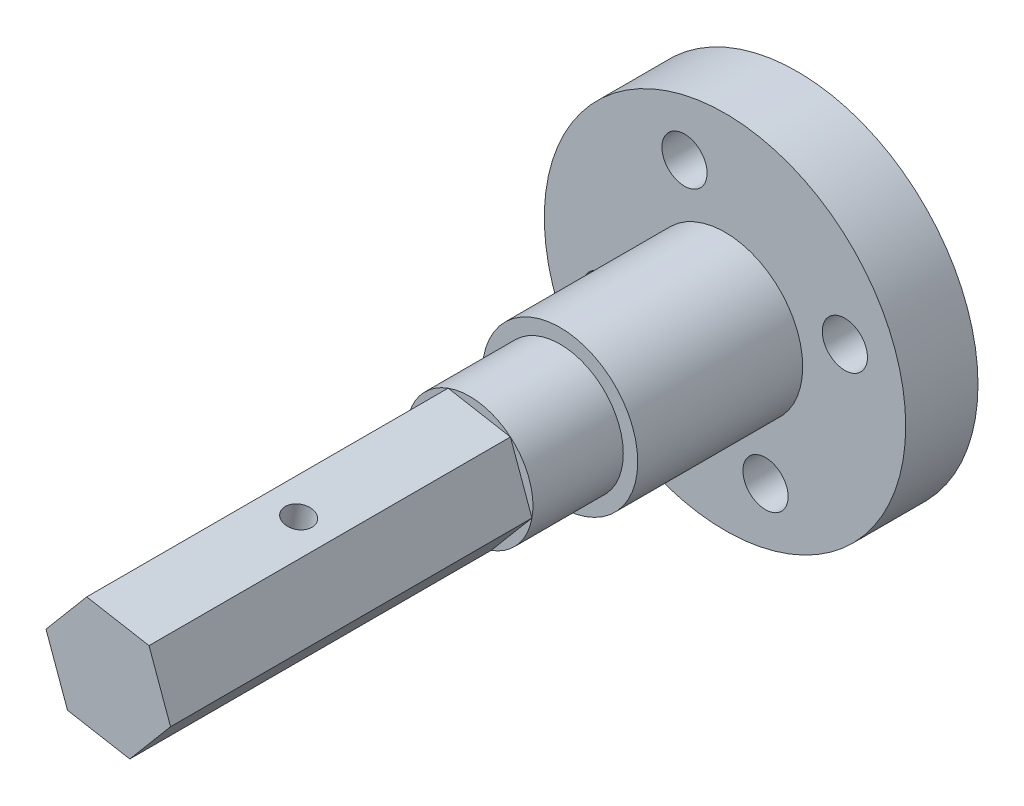
SolidWorks part; units mm, degrees
ref_plane "Plan de face" through (0, 0, 0) normal (0, 0, 1) x (1, 0, 0)
ref_plane "Plan de dessus" through (0, 0, 0) normal (0, 1, 0) x (1, 0, 0)
ref_plane "Plan de droite" through (0, 0, 0) normal (1, 0, 0) x (0, 0, -1)
sketch "Esquisse1" plane through (0, 0, 0) normal (0, 0, 1) x (1, 0, 0)
  circle A0 centre (0, 0) radius 10
  dimension "D1" = 20
extrude "Boss.-Extru.1" add sketch "Esquisse1" along normal blind 4
sketch "Esquisse2" plane through (0, 0, 4) normal (0, 0, 1) x (1, 0, 0)
  circle A0 centre (0, 0) radius 3.5
  dimension "D1" = 7
extrude "Boss.-Extru.2" add sketch "Esquisse2" along normal blind 14.13
sketch "Esquisse3" plane through (0, 0, 18.13) normal (0, 0, 1) x (1, 0, 0)
  line L1 (-1.1905, 3.2913) -> (-3.4456, 0.6147)
  line L2 (-3.4456, 0.6147) -> (-2.2551, -2.6766)
  line L3 (-2.2551, -2.6766) -> (1.1905, -3.2913)
  line L4 (1.1905, -3.2913) -> (3.4456, -0.6147)
  line L5 (3.4456, -0.6147) -> (2.2551, 2.6766)
  line L6 (2.2551, 2.6766) -> (-1.1905, 3.2913)
  circle A0 centre (0, 0) radius 3.0311 construction
extrude "Boss.-Extru.3" add sketch "Esquisse3" along normal blind 20
sketch "Esquisse4" plane through (0, 0, 0) normal (0, 0, -1) x (-1, 0, 0)
  circle A0 centre (2.2414, 6.6315) radius 1.25
  circle A1 centre (-6.6315, 2.2414) radius 1.25
  circle A2 centre (6.6315, -2.2414) radius 1.25
  circle A3 centre (-2.2414, -6.6315) radius 1.25
extrude "Enlèv. mat.-Extru.1" cut sketch "Esquisse4" against normal blind 100
sketch "Esquisse5" plane through (0.5323, 2.984, 0) normal (0.1756, 0.9845, 0) x (0.9845, -0.1756, 0)
  line L0 (1.75, -18.13) -> (-1.75, -18.13) construction
  circle A0 centre (0, -28.1279) radius 0.75
  point P5 (0, 0)
  dimension "D1" = 1.5
  dimension "D2" = 9.9979
extrude "Enlèv. mat.-Extru.2" cut sketch "Esquisse5" against normal blind 14
sketch "Esquisse6" plane through (0, 0, 0) normal (0, 0, -1) x (-1, 0, 0)
  circle A0 centre (0, 0) radius 2.1271
extrude "Enlèv. mat.-Extru.3" cut sketch "Esquisse6" against normal blind 1.5
sketch "Esquisse7" plane through (0, 0, 4) normal (0, 0, 1) x (1, 0, 0)
  circle A0 centre (0, 0) radius 4.3
  circle A1 centre (0, 0) radius 3.5 construction
  circle A2 centre (0, 0) radius 3.5
  dimension "D1" = 8.6
extrude "Boss.-Extru.4" add sketch "Esquisse7" along normal blind 9.13
